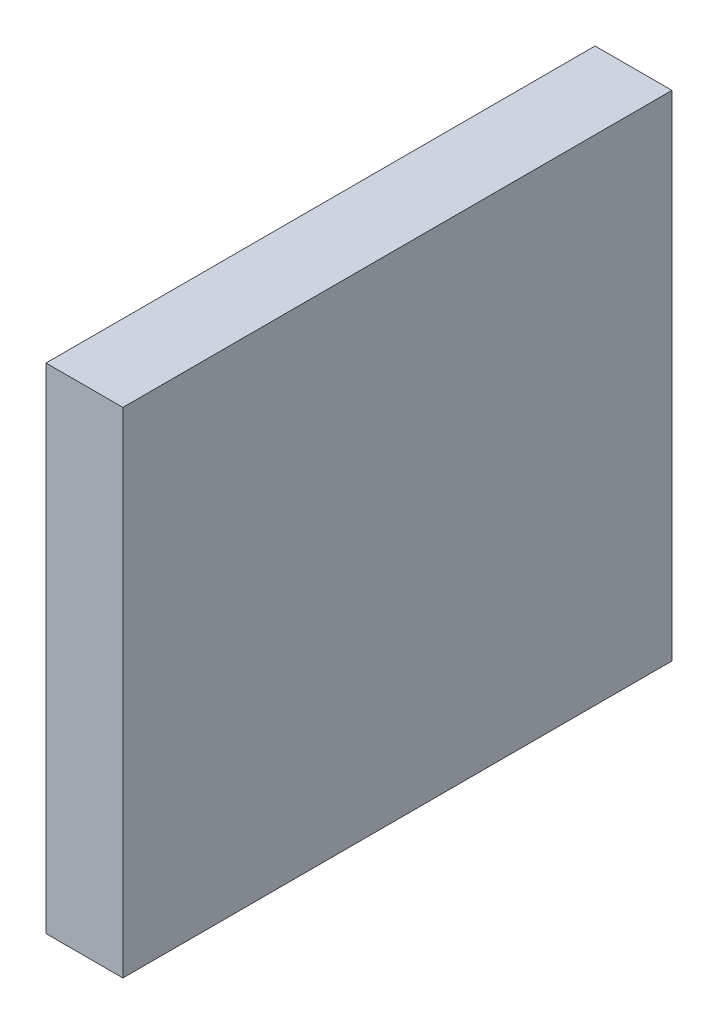
SolidWorks part; units mm, degrees
ref_plane "Front Plane" through (0, 0, 0) normal (0, 0, 1) x (1, 0, 0)
ref_plane "Top Plane" through (0, 0, 0) normal (0, 1, 0) x (1, 0, 0)
ref_plane "Right Plane" through (0, 0, 0) normal (1, 0, 0) x (0, 0, -1)
sketch "Sketch1" plane through (0, 0, 0) normal (1, 0, 0) x (0, 0, -1)
  line L1 (0, 0) -> (50, 0)
  line L2 (0, 0) -> (0, 45)
  line L3 (0, 45) -> (50, 45)
  line L4 (50, 0) -> (50, 45)
  dimension "D1" = 50
  dimension "D2" = 45
extrude "Boss-Extrude1" add sketch "Sketch1" along normal blind 7
